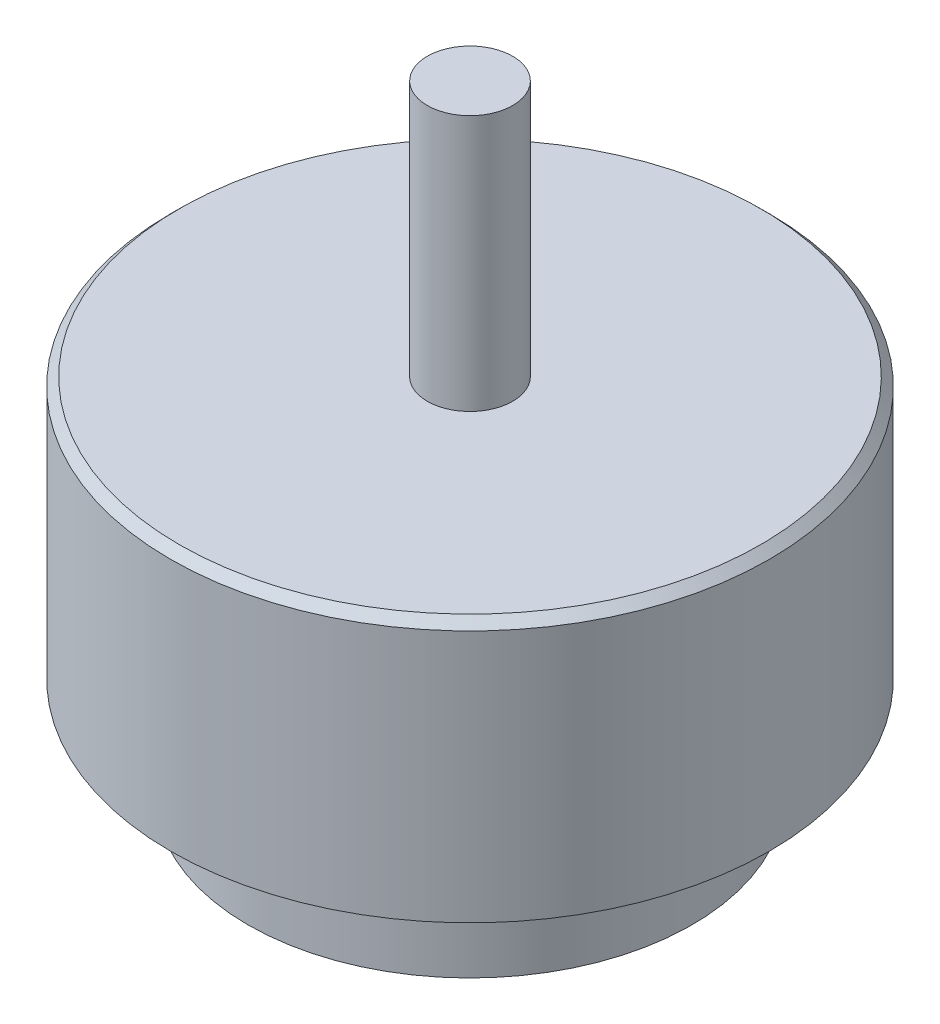
SolidWorks part; units mm, degrees
material "6061-T6 (SS)"
ref_plane "Front Plane" through (0, 0, 0) normal (0, 0, 1) x (1, 0, 0)
ref_plane "Top Plane" through (0, 0, 0) normal (0, 1, 0) x (1, 0, 0)
ref_plane "Right Plane" through (0, 0, 0) normal (1, 0, 0) x (0, 0, -1)
sketch "Sketch1" plane through (0, 0, 0) normal (0, 1, 0) x (1, 0, 0)
  circle A0 centre (0, 0) radius 13
  dimension "D1" = 26
extrude "Boss-Extrude1" add sketch "Sketch1" along normal blind 6
sketch "Sketch2" plane through (0, 6, 0) normal (0, 1, 0) x (1, 0, 0)
  circle A0 centre (0, 0) radius 17.53
  dimension "D1" = 35.06
extrude "Boss-Extrude2" add sketch "Sketch2" along normal blind 15.3
sketch "Sketch3" plane through (0, 21.3, 0) normal (0, 1, 0) x (1, 0, 0)
  circle A0 centre (0, 0) radius 2.5
  dimension "D1" = 5
extrude "Boss-Extrude3" add sketch "Sketch3" along normal blind 15
chamfer "Chamfer1" distance 0.5 angle 45 1 edges at (0, 21.3, 17.53)
sketch "Sketch4" plane through (0, 0, 0) normal (0, -1, 0) x (1, 0, 0)
  circle A0 centre (0, 0) radius 7
  dimension "D1" = 14
extrude "Cut-Extrude1" cut sketch "Sketch4" against normal blind 6
